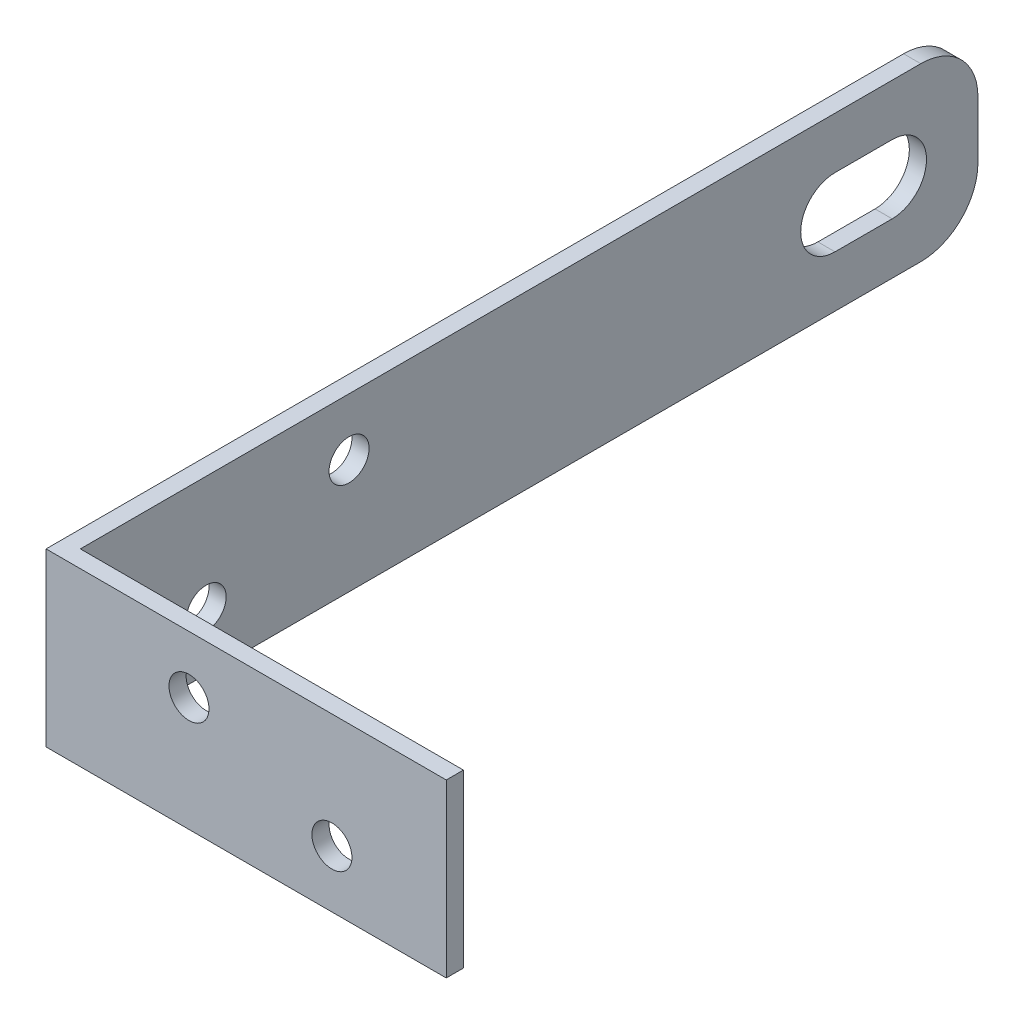
SolidWorks part; units mm, degrees
ref_plane "Спереди" through (0, 0, 0) normal (0, 0, 1) x (1, 0, 0)
ref_plane "Сверху" through (0, 0, 0) normal (0, 1, 0) x (1, 0, 0)
ref_plane "Справа" through (0, 0, 0) normal (1, 0, 0) x (0, 0, -1)
sketch "Эскиз1" plane through (0, 0, 0) normal (0, 1, 0) x (1, 0, 0)
  line L0 (0, 0) -> (70, 0)
  line L1 (0, 0) -> (0, 120)
  line L2 (0, 120) -> (0, 160)
extrude "Вытянуть-Тонкостенный1" add sketch "Эскиз1" along normal blind 30 thin thin type one direction wall 3
sketch "Эскиз2" plane through (0, 0, 0) normal (-1, 0, 0) x (0, 0, 1)
  circle A1 centre (-50, 20) radius 3.5
  circle A2 centre (-25, 10) radius 3.5
extrude "Вырез-Вытянуть1" cut sketch "Эскиз2" against normal through all
sketch "Эскиз3" plane through (0, 0, 0) normal (0, 0, 1) x (1, 0, 0)
  circle A0 centre (25, 20) radius 3.5
  circle A1 centre (50, 10) radius 3.5
extrude "Вырез-Вытянуть2" cut sketch "Эскиз3" against normal through all
sketch "Эскиз4" plane through (0, 0, 0) normal (-1, 0, 0) x (0, 0, 1)
  line L0 (-145, 21) -> (-135, 21)
  line L1 (-145, 9) -> (-135, 9)
  line L2 (-160, 20) -> (-160, 30)
  line L3 (-160, 30) -> (-160, 0) construction
  line L4 (-160, 30) -> (-150, 30)
  line L5 (0, 30) -> (-160, 30) construction
  line L6 (-160, 10) -> (-160, 0)
  line L7 (-160, 0) -> (-150, 0)
  line L8 (-120, 0) -> (-160, 0) construction
  arc A0 (-145, 21) -> (-145, 9) centre (-145, 15) ccw
  arc A1 (-135, 21) -> (-135, 9) centre (-135, 15) cw
  arc A2 (-160, 20) -> (-150, 30) centre (-150, 20) cw
  arc A3 (-160, 10) -> (-150, 0) centre (-150, 10) ccw
extrude "Вырез-Вытянуть3" cut sketch "Эскиз4" against normal through all
